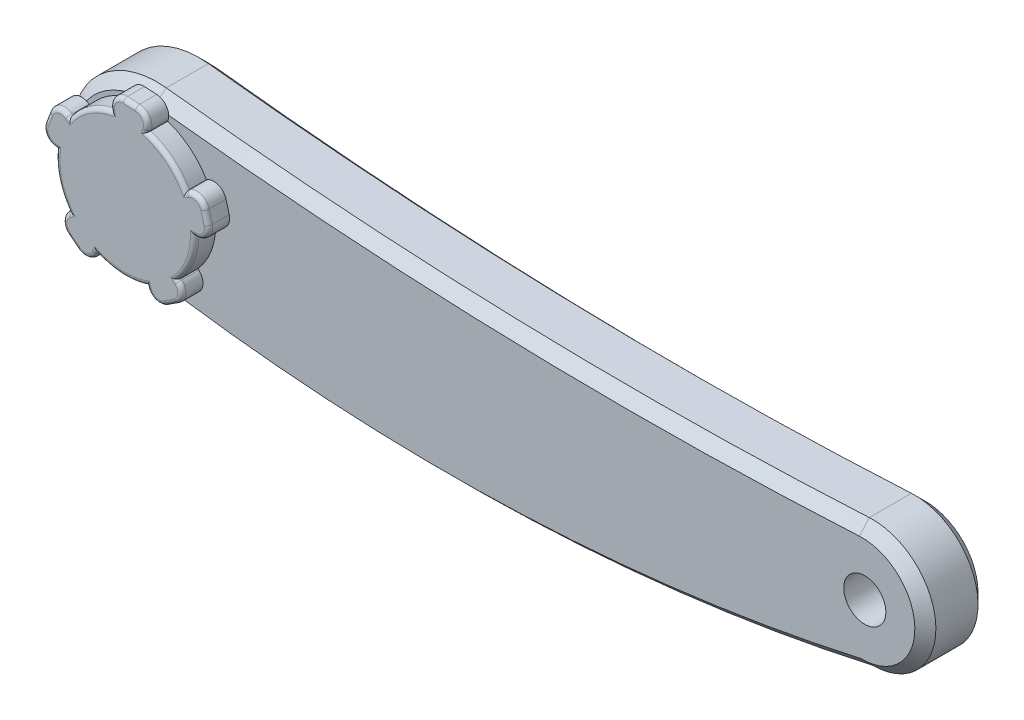
SolidWorks part; units mm, degrees
material "PE High Density"
ref_plane "Front Plane" through (0, 0, 0) normal (0, 0, 1) x (1, 0, 0)
ref_plane "Top Plane" through (0, 0, 0) normal (0, 1, 0) x (1, 0, 0)
ref_plane "Right Plane" through (0, 0, 0) normal (1, 0, 0) x (0, 0, -1)
sketch "Sketch1" plane through (0, 0, 0) normal (0, 0, 1) x (1, 0, 0)
  line L0 (-85, 0) -> (85, 0) construction
  circle A0 centre (85, 0) radius 15
  circle A1 centre (-85, 0) radius 20
  arc A2 (84.1861, 14.9779) -> (-82.7465, 19.8726) centre (29.9265, 1013.5048) cw
  arc A3 (-88.3169, -19.723) -> (85, -15) centre (-13.6872, 424.0454) ccw
  point P4 (0, 0)
  dimension "D2" = 40
  dimension "D3" = 30
  dimension "D4" = 450
  dimension "D5" = 1000
  dimension "D1" = 170
extrude "Boss-Extrude1" add sketch "Sketch1" along normal mid plane 15
chamfer "Chamfer1" distance 2.5 angle 45 8 edges at (99.9945, 0.4071, -7.5) (99.9945, 0.4071, 7.5) (0.6174, 13.9344, -7.5) (0.6174, 13.9344, 7.5) (-104.805, 2.7862, -7.5) (-104.805, 2.7862, 7.5) (-1.4288, -25.7876, -7.5) (-1.4288, -25.7876, 7.5)
sketch "Sketch2" plane through (0, 0, 7.5) normal (0, 0, 1) x (1, 0, 0)
  circle A0 centre (-85, 0) radius 16.5
  dimension "D1" = 33
extrude "Boss-Extrude2" add sketch "Sketch2" along normal blind 5
sketch "Sketch3" plane through (0, 0, 12.5) normal (0, 0, 1) x (1, 0, 0)
  line L0 (-85, 0) -> (-68.2042, 0)
  line L2 (-65.3064, 3.7765) -> (-66.0566, 6.5763)
  line L3 (-70.4544, 8.3979) -> (-85, 0)
  line L4 (-85, 0) -> (-65.6815, 5.1764) construction
  line L5 (-72.5183, -11.2386) -> (-85, 0)
  line L6 (-75.3227, -17.5628) -> (-72.8917, -15.9841)
  line L7 (-85, 0) -> (-79.8098, -15.9738)
  line L8 (-91.8315, -15.3438) -> (-85, 0)
  line L9 (-98.7127, -14.6308) -> (-96.4601, -16.455)
  line L10 (-85, 0) -> (-98.5881, -9.8724)
  line L11 (-101.7038, 1.7556) -> (-85, 0)
  line L12 (-103.1522, 8.5204) -> (-104.191, 5.8143)
  line L13 (-85, 0) -> (-98.5881, 9.8724)
  line L14 (-88.4921, 16.4288) -> (-85, 0)
  line L15 (-82.506, 19.8967) -> (-85.4006, 20.0484)
  line L16 (-85, 0) -> (-79.8098, 15.9738)
  arc A0 (-72.8917, -15.9841) -> (-72.5183, -11.2386) centre (-74.5256, -13.4681) ccw
  arc A1 (-65.3064, 3.7765) -> (-68.2042, 0) centre (-68.2042, 3) cw
  arc A2 (-66.0566, 6.5763) -> (-70.4544, 8.3979) centre (-68.9544, 5.7998) ccw
  arc A3 (-75.3227, -17.5628) -> (-79.8098, -15.9738) centre (-76.9566, -15.0467) cw
  arc A4 (-96.4601, -16.455) -> (-91.8315, -15.3438) centre (-94.5721, -14.1236) ccw
  arc A5 (-98.7127, -14.6308) -> (-98.5881, -9.8724) centre (-96.8248, -12.2994) cw
  arc A6 (-104.191, 5.8143) -> (-101.7038, 1.7556) centre (-101.3903, 4.7392) ccw
  arc A7 (-103.1522, 8.5204) -> (-98.5881, 9.8724) centre (-100.3515, 7.4453) cw
  arc A8 (-85.4006, 20.0484) -> (-88.4921, 16.4288) centre (-85.5576, 17.0526) ccw
  arc A9 (-82.506, 19.8967) -> (-79.8098, 15.9738) centre (-82.663, 16.9009) cw
  circle A10 centre (-85, 0) radius 2
  point P10 (-67.0685, 10.3528)
  point P36 (-85, 0)
  circle M8 centre (-85, 0) radius 16.5
  dimension "D3" = 3
  dimension "D5" = 4
  dimension "D1" = 30
  dimension "D2" = 20
  dimension "D4" = 5
extrude "Boss-Extrude3" add sketch "Sketch3" against normal blind 5 contours A9 L15 A8 L14 L16 M8 | A10 L16 L14 M8 | A10 L4 L3 M8 | L4 A10 L0 M8 | L4 L0 A1 L2 M8 | L4 L2 A2 L3 M8 | A10 L7 L5 M8 | A3 L6 A0 L5 L7 M8 | A10 L10 L8 M8 | A5 L9 A4 L8 L10 M8 | A7 L12 A6 L11 L13 M8 | A10 L13 L11 M8
fillet "Fillet1" radius 1 30 edges at (-88.4613, 16.2841, 12.5) (-87.8388, 19.0009, 12.5) (-83.9533, 19.9726, 12.5) (-80.1906, 18.6001, 12.5) (-79.8555, 15.8331, 12.5) (-74.6162, 12.8229, 12.5) (-70.5825, 8.324, 12.5) (-67.8063, 8.5715, 12.5) (-65.6815, 5.1764, 12.5) (-65.8241, 1.1737, 12.5) (-68.3521, 0, 12.5) (-69.5959, -5.9131, 12.5) (-72.6282, -11.1396, 12.5) (-71.5349, -13.7034, 12.5) (-74.1072, -16.7734, 12.5) (-77.958, -17.8747, 12.5) (-79.8555, -15.8331, 12.5) (-85.8635, -16.4774, 12.5) (-91.7713, -15.2086, 12.5) (-93.8718, -17.0407, 12.5) (-97.5864, -15.5429, 12.5) (-99.8237, -12.2209, 12.5) (-98.4685, -9.7854, 12.5) (-100.9378, -4.2705, 12.5) (-101.5567, 1.7402, 12.5) (-103.9482, 3.1717, 12.5) (-103.6716, 7.1674, 12.5) (-101.2035, 10.3218, 12.5) (-98.4685, 9.7854, 12.5) (-93.9865, 13.8381, 12.5)
sketch "Sketch4" plane through (0, 0, 7.5) normal (0, 0, 1) x (1, 0, 0)
  circle A0 centre (85.6153, 0) radius 5
  dimension "D1" = 10
extrude "Cut-Extrude1" cut sketch "Sketch4" against normal blind 10
sketch "Sketch5" plane through (0, 0, -7.5) normal (0, 0, -1) x (-1, 0, 0)
  circle A0 centre (85, 0) radius 5
  dimension "D1" = 10
extrude "Boss-Extrude4" add sketch "Sketch5" along normal blind 10
